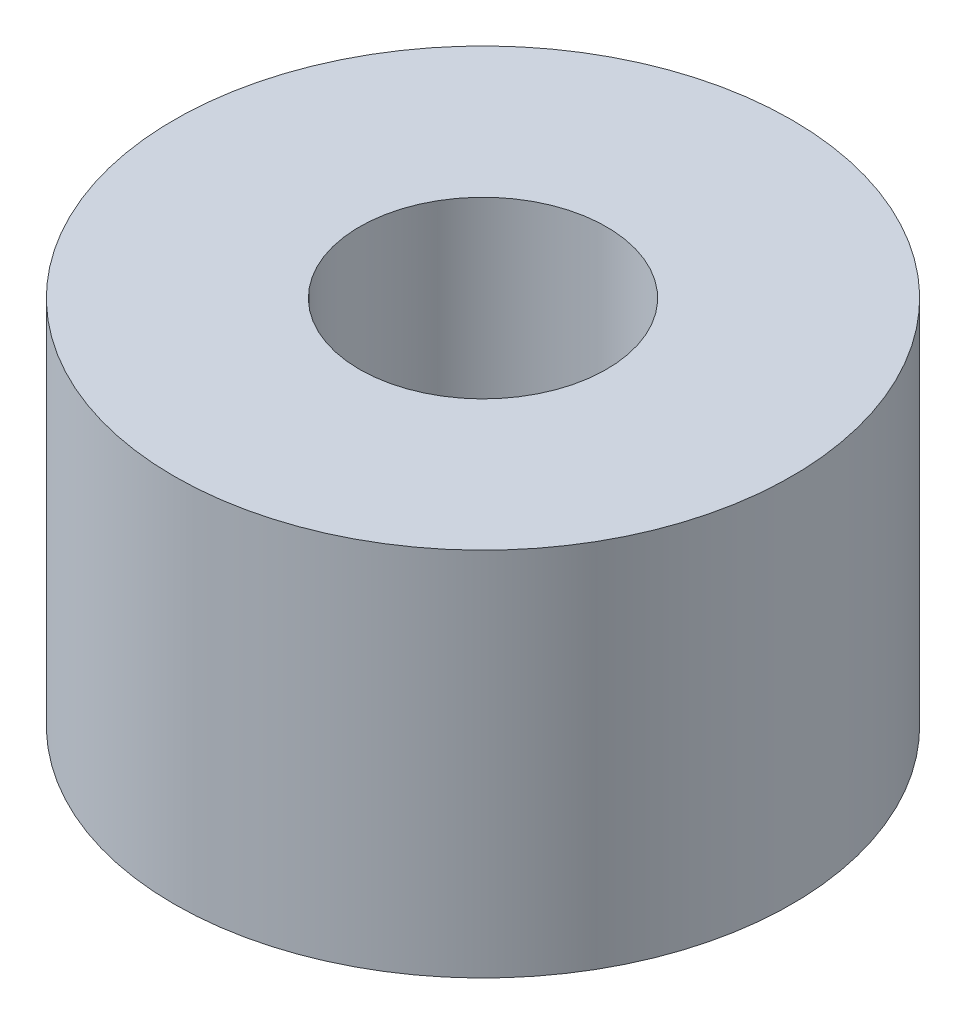
SolidWorks part; units mm, degrees
ref_plane "Front Plane" through (0, 0, 0) normal (0, 0, 1) x (1, 0, 0)
ref_plane "Top Plane" through (0, 0, 0) normal (0, 1, 0) x (1, 0, 0)
ref_plane "Right Plane" through (0, 0, 0) normal (1, 0, 0) x (0, 0, -1)
sketch "Sketch1" plane through (0, 0, 0) normal (0, 1, 0) x (1, 0, 0)
  circle A0 centre (0, 0) radius 2
  circle A1 centre (0, 0) radius 5
  dimension "D1" = 4
  dimension "D2" = 3
extrude "Boss-Extrude1" add sketch "Sketch1" along normal blind 6
